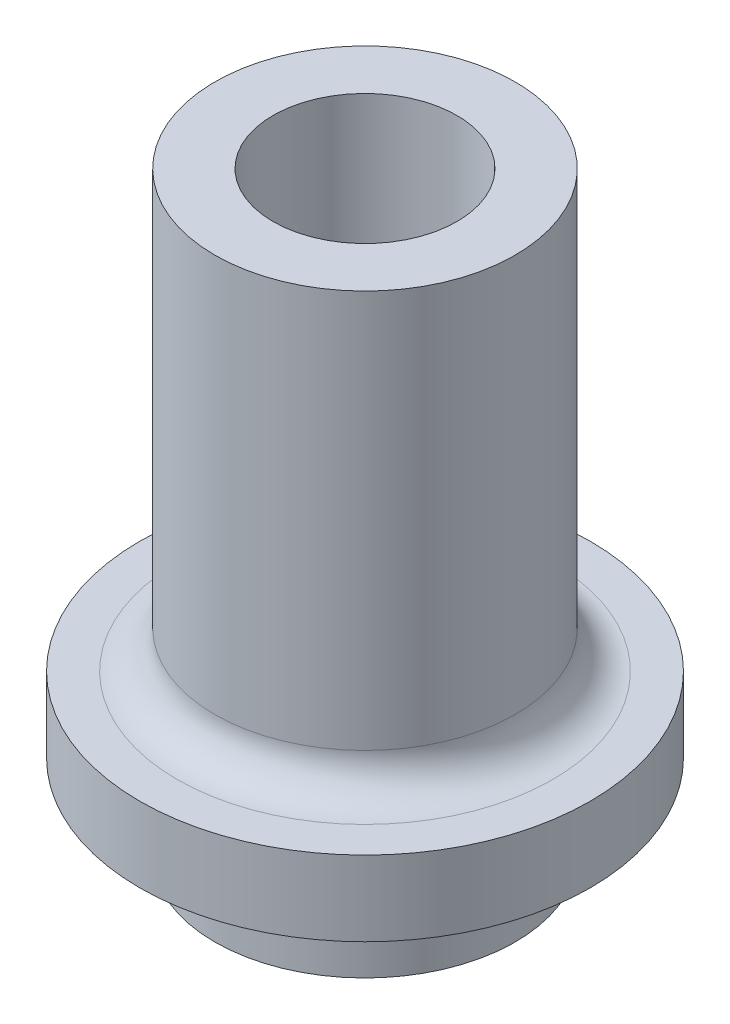
SolidWorks part; units mm, degrees
ref_plane "Front" through (0, 0, 0) normal (0, 0, 1) x (1, 0, 0)
ref_plane "Top" through (0, 0, 0) normal (0, 1, 0) x (1, 0, 0)
ref_plane "Right" through (0, 0, 0) normal (1, 0, 0) x (0, 0, -1)
sketch "Sketch1" plane through (0, 0, 0) normal (0, 1, 0) x (1, 0, 0)
  line L0 (-1.12, 1.1705) -> (1.12, 1.1705)
  circle A0 centre (0, 0) radius 4
  arc A1 (-1.12, 1.1705) -> (1.12, 1.1705) centre (0, 0) ccw
  dimension "D1" = 3.24
  dimension "D3" = 8
  dimension "D2" = 2.24
extrude "Boss-Extrude1" add sketch "Sketch1" along normal blind 9.25
sketch "Sketch2" plane through (0, 9.25, 0) normal (0, 1, 0) x (1, 0, 0)
  circle A0 centre (0, 0) radius 4
  circle A1 centre (0, 0) radius 4 construction
extrude "Boss-Extrude2" add sketch "Sketch2" along normal blind 1
sketch "Sketch3" plane through (0, 10.25, 0) normal (0, 1, 0) x (1, 0, 0)
  circle A0 centre (0, 0) radius 2.45
  circle A2 centre (0, 0) radius 4
  circle A3 centre (0, 0) radius 4
  dimension "D1" = 4.9
  dimension "D2" = 0
extrude "Boss-Extrude3" add sketch "Sketch3" along normal blind 5.6
sketch "Sketch5" plane through (0, 2.25, 0) normal (0, 1, 0) x (1, 0, 0)
  line L0 (1.12, 1.1705) -> (-1.12, 1.1705) construction
  line L1 (1.12, 1.1705) -> (-1.12, 1.1705)
  circle A0 centre (0, 0) radius 6
  arc A1 (-1.12, 1.1705) -> (1.12, 1.1705) centre (0, 0) ccw construction
  arc A2 (-1.12, 1.1705) -> (1.12, 1.1705) centre (0, 0) ccw
  dimension "D1" = 12
extrude "Boss-Extrude4" add sketch "Sketch5" along normal blind 2
fillet "Fillet1" radius 1 1 edges at (0, 4.25, 4)
